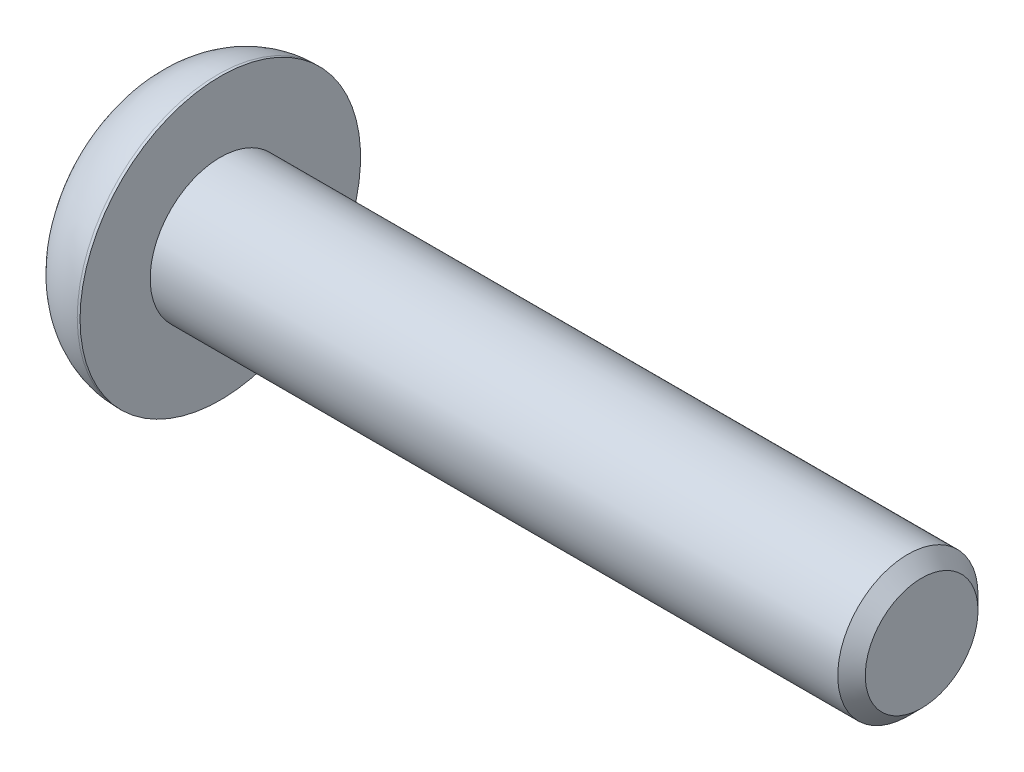
SolidWorks part; units mm, degrees
ref_plane "Front Plane" through (0, 0, 0) normal (0, 0, 1) x (1, 0, 0)
ref_plane "Top Plane" through (0, 0, 0) normal (0, 1, 0) x (1, 0, 0)
ref_plane "Right Plane" through (0, 0, 0) normal (1, 0, 0) x (0, 0, -1)
ref_plane "Плоскость4" through (0, 0, 0) normal (0, 0, -1) x (-1, 0, 0)
sketch "Эскиз1" plane through (0, 0, 0) normal (0, 0, -1) x (-1, 0, 0)
  line L0 (-2.8, 5) -> (-2.8, 0)
  line L1 (-2.8, 0) -> (0, 0)
  line L2 (0, 0) -> (0, 5)
  line L3 (0, 5) -> (-2.8, 5)
  line L4 (-2.8, 0) -> (0, 0) construction
revolve "Повернуть1" add sketch "Эскиз1" angle 360 about L4
sketch "Эскиз2" plane through (2.8, 0, 0) normal (1, 0, 0) x (0, 0, -1)
  circle A0 centre (0, 0) radius 2.5
extrude "Бобышка-Вытянуть1" add sketch "Эскиз2" along normal blind 25
sketch "Эскиз3" plane through (0, 0, 0) normal (-1, 0, 0) x (0, 0, 1)
  line L0 (0, 1.7321) -> (-1.5, 0.866)
  line L1 (-1.5, 0.866) -> (-1.5, -0.866)
  line L2 (-1.5, -0.866) -> (0, -1.7321)
  line L3 (0, -1.7321) -> (1.5, -0.866)
  line L4 (1.5, -0.866) -> (1.5, 0.866)
  line L5 (1.5, 0.866) -> (0, 1.7321)
extrude "Вырез-Вытянуть1" cut sketch "Эскиз3" against normal blind 1.82
hole_wizard "Диаметр отверстия Ø3.0 (3)1" positions "Эскиз5" profile "Эскиз4" hole size "Ø3.0" standard "Ansi Metric"
sketch "Эскиз5" plane through (1.82, 0, 0) normal (-1, 0, 0) x (0, 0, 1)
  point P0 (0, 0)
sketch "Эскиз4" plane through (1.82, 0, 0) normal (0, 1, 0) x (0, 0, 1)
  line L0 (0, 0) -> (0, 0.98)
  line L1 (0, 0.98) -> (1.5, 0.114)
  line L2 (1.5, 0.114) -> (1.5, 0)
  line L5 (1.5, 0) -> (0, 0)
  line L10 (0, 0.98) -> (-1.5, 0.114) construction
  line L11 (0, -6.35) -> (0, 107.95) construction
  dimension "Диаметр отверстия" = 3
  dimension "Глубина отверстия" = 0.114
  dimension "Угол заточки сверла" = 120
chamfer "Фаска1" distance 0.4905 angle 45 1 edges at (27.8, 0, -2.5)
fillet "Скругление1" radius 2.7 1 edges at (0, 0, 5)
